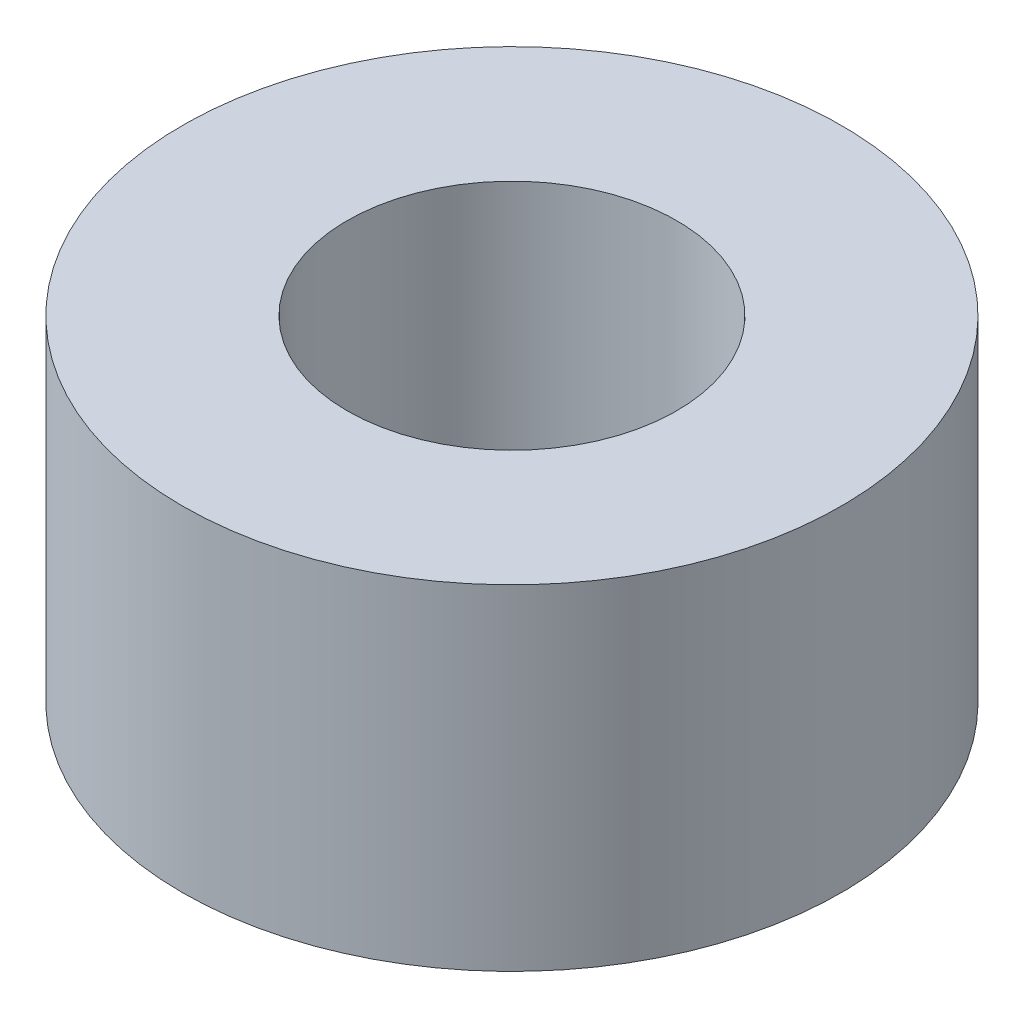
SolidWorks part; units mm, degrees
ref_plane "Front" through (0, 0, 0) normal (0, 0, 1) x (1, 0, 0)
ref_plane "Top" through (0, 0, 0) normal (0, 1, 0) x (1, 0, 0)
ref_plane "Right" through (0, 0, 0) normal (1, 0, 0) x (0, 0, -1)
sketch "Sketch1" plane through (0, 0, 0) normal (0, 1, 0) x (1, 0, 0)
  circle A0 centre (0, 0) radius 1.25
  circle A1 centre (0, 0) radius 2.5
extrude "Boss-Extrude1" add sketch "Sketch1" along normal blind 2.54 contours A1 A0
